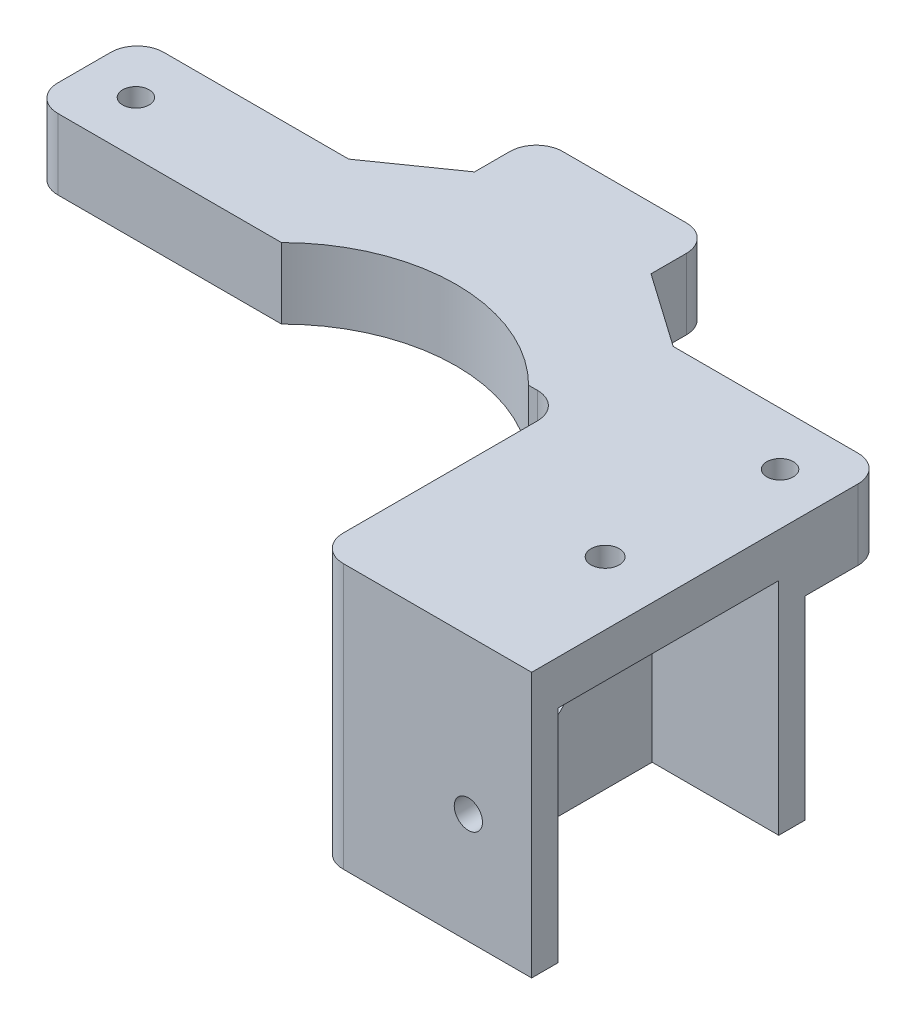
SolidWorks part; units mm, degrees
ref_plane "Front Plane" through (0, 0, 0) normal (0, 0, 1) x (1, 0, 0)
ref_plane "Top Plane" through (0, 0, 0) normal (0, 1, 0) x (1, 0, 0)
ref_plane "Right Plane" through (0, 0, 0) normal (1, 0, 0) x (0, 0, -1)
sketch "Sketch1" plane through (0, 0, 0) normal (0, 1, 0) x (1, 0, 0)
  point P0 (19.9354, 20.5827)
  line B0 (39.209, 44.4444) -> (22.0404, 42.2474)
  line B1 (45.8541, 73.4809) -> (45.8541, 51.994)
  line B2 (42.0529, 77.2821) -> (-35.0361, 77.2821)
  line B3 (-38.8372, 73.4809) -> (-38.8372, 51.994)
  line B4 (-32.1921, 44.4444) -> (-15.0236, 42.2474)
  arc B5 (19.8482, 42.7521) -> (-12.8313, 42.7521) centre (3.5084, 38.4289) ccw
  circle B6 centre (-16.4916, 46.356) radius 2.5
  circle B7 centre (-32.9916, 71.4109) radius 2.5
  circle B8 centre (40.0084, 71.4109) radius 2.5
  circle B9 centre (23.5084, 46.356) radius 2.5
  arc B10 (39.209, 44.4444) -> (45.8541, 51.994) centre (38.2429, 51.994) ccw
  arc B11 (-35.0361, 77.2821) -> (-38.8372, 73.4809) centre (-35.0361, 73.4809) ccw
  arc B12 (-38.8372, 51.994) -> (-32.1921, 44.4444) centre (-31.2261, 51.994) ccw
sketch_block_instance "ps3_eye_screws-1"
sketch_block "ps3_eye_screws"
sketch "Sketch2" plane through (0, 0, 0) normal (0, 1, 0) x (1, 0, 0)
  line L0 (3.5084, 38.4024) -> (3.5084, 55.3309) construction
  line L4 (-38.8372, 64.4109) -> (-14.8764, 64.4109)
  line L5 (-32.9916, 71.4109) -> (40.0084, 71.4109) construction
  line L6 (-32.9916, 71.4109) -> (-32.9916, 58.4109) construction
  line L7 (-32.9916, 58.4109) -> (40.0084, 58.4109) construction
  line L8 (40.0084, 71.4109) -> (40.0084, 58.4109) construction
  line L9 (-38.8372, 73.4809) -> (-38.8372, 51.994) construction
  line L10 (-14.8764, 64.4109) -> (-6.4916, 70.2821)
  line L11 (-6.4916, 70.2821) -> (-6.4916, 77.2821)
  line L12 (42.0529, 77.2821) -> (-35.0361, 77.2821) construction
  line L13 (-6.4916, 77.2821) -> (13.5084, 77.2821)
  line L14 (13.5084, 77.2821) -> (13.5084, 70.2821)
  line L15 (13.5084, 70.2821) -> (21.8933, 64.4109)
  line L16 (21.8933, 64.4109) -> (45.8541, 64.4109)
  line L17 (45.8541, 73.4809) -> (45.8541, 51.994) construction
  line L18 (45.8541, 64.4109) -> (45.8541, 52.4109)
  line L19 (45.8541, 52.4109) -> (17.5084, 52.4109)
  line L20 (-10.4916, 52.4109) -> (-38.8372, 52.4109)
  line L21 (-38.8372, 52.4109) -> (-38.8372, 64.4109)
  line L22 (3.5084, 55.3309) -> (3.5084, 77.2821) construction
  line L23 (-6.4916, 70.2821) -> (13.5084, 70.2821) construction
  line L24 (-32.9916, 58.4109) -> (-38.8372, 58.4109) construction
  line L25 (40.0084, 58.4109) -> (45.8541, 58.4109) construction
  circle A2 centre (-32.9916, 58.4109) radius 1.5
  circle A3 centre (40.0084, 58.4109) radius 1.5
  arc A4 (19.8482, 42.7521) -> (-12.8313, 42.7521) centre (3.5084, 38.4289) ccw construction
  arc A5 (-10.4916, 52.4109) -> (17.5084, 52.4109) centre (3.5084, 38.4024) cw
  point P27 (8.08, 39.4837)
  point P33 (3.5084, 42.9446)
  point P34 (3.5084, 38.4024)
  dimension "D1" = 3
  dimension "D7" = 28
  dimension "D8" = 19.805
  dimension "D2" = 13
  dimension "D3" = 145
  dimension "D4" = 145
  dimension "D5" = 20
  dimension "D6" = 12
  dimension "D9" = 7
extrude "Boss-Extrude1" add sketch "Sketch2" along normal blind 8
ref_plane "Plane1" through (0, 8, 0) normal (0, -1, 0) x (-1, 0, 0)
sketch "Sketch11" plane through (0, 8, 0) normal (0, -1, 0) x (-1, 0, 0)
  line L1 (14.4916, 55.4109) -> (38.8372, 55.4109)
  line L2 (14.4916, 55.4109) -> (14.4916, 24.4109)
  line L3 (14.4916, 24.4109) -> (38.8372, 24.4109)
  line L4 (38.8372, 55.4109) -> (38.8372, 24.4109)
  line L5 (38.8372, 73.4809) -> (38.8372, 51.994) construction
  circle A0 centre (32.9916, 58.4109) radius 1.5 construction
  point P6 (38.8372, 52.4109)
  point P8 (0, 0)
  point P9 (38.8372, 52.4109)
  point P10 (38.8372, 55.4109)
  dimension "D2" = 3
  dimension "D1" = 5
  dimension "D3" = 31
extrude "Boss-Extrude4" add sketch "Sketch11" along normal blind 30
sketch "Sketch12" plane through (-38.8372, 0, 0) normal (-1, 0, 0) x (0, 0, 1)
  line L0 (-24.4109, -22) -> (-55.4109, -22) construction
  line L1 (-52.4109, -22) -> (-27.4109, -22)
  line L2 (-52.4109, -22) -> (-52.4109, 3)
  line L3 (-52.4109, 3) -> (-27.4109, 3)
  line L4 (-27.4109, -22) -> (-27.4109, 3)
  line L5 (-55.4109, -22) -> (-55.4109, 0) construction
  dimension "D1" = 25
  dimension "D2" = 25
  dimension "D3" = 3
extrude "Cut-Extrude7" cut sketch "Sketch12" against normal offset from surface (14.3456 mm away) 10 up to face at (-14.4916, -4.6667, -44.0776)
sketch "Sketch13" plane through (-14.4916, 0, 0) normal (1, 0, 0) x (0, 0, -1)
  line L0 (52.4109, -22) -> (27.4109, 3) construction
  circle A0 centre (39.9109, -9.5) radius 3.1
  dimension "D1" = 6.2
extrude "Cut-Extrude8" cut sketch "Sketch13" against normal up to next
sketch "Sketch14" plane through (-14.4916, 0, 0) normal (1, 0, 0) x (0, 0, -1)
  circle A0 centre (39.9109, -9.5) radius 5
  dimension "D1" = 10
extrude "Cut-Extrude9" cut sketch "Sketch14" against normal blind 5.5
sketch "Sketch15" plane through (0, 0, -24.4109) normal (0, 0, 1) x (1, 0, 0)
  line L0 (-31.6644, -22) -> (-31.6644, 3) construction
  line L1 (-24.4916, 3) -> (-38.8372, 3) construction
  line L2 (-14.4916, -22) -> (-38.8372, -22) construction
  circle A0 centre (-31.6644, -9.5) radius 1.6
  point P6 (-31.6644, 3)
  point P9 (-34.4877, -22)
  dimension "D1" = 3.2
extrude "Cut-Extrude10" cut sketch "Sketch15" against normal blind 5.5
sketch "Sketch16" plane through (0, 8, 0) normal (0, 1, 0) x (1, 0, 0)
  line L0 (-31.6644, 52.4109) -> (-31.6644, 27.4109) construction
  line L1 (-24.4916, 52.4109) -> (-38.8372, 52.4109) construction
  line L2 (-24.4916, 27.4109) -> (-38.8372, 27.4109) construction
  circle A0 centre (-31.6644, 39.9109) radius 1.6
  dimension "D1" = 3.2
extrude "Cut-Extrude11" cut sketch "Sketch16" against normal up to next contours A0
sketch "Sketch17" plane through (0, 0, 0) normal (0, -1, 0) x (1, 0, 0)
  line L0 (-38.8372, -55.4109) -> (-14.4916, -55.4109) construction
  line L1 (-31.2595, -61.4109) -> (-29.5275, -58.4109)
  line L2 (-29.5275, -58.4109) -> (-31.2595, -55.4109)
  line L3 (-31.2595, -55.4109) -> (-34.7236, -55.4109)
  line L4 (-34.7236, -55.4109) -> (-36.4557, -58.4109)
  line L5 (-36.4557, -58.4109) -> (-34.7236, -61.4109)
  line L6 (-34.7236, -61.4109) -> (-31.2595, -61.4109)
  line L8 (38.2764, -61.4109) -> (41.7405, -61.4109)
  line L9 (41.7405, -61.4109) -> (43.4725, -58.4109)
  line L10 (43.4725, -58.4109) -> (41.7405, -55.4109)
  line L11 (41.7405, -55.4109) -> (38.2764, -55.4109)
  line L12 (38.2764, -55.4109) -> (36.5443, -58.4109)
  line L13 (36.5443, -58.4109) -> (38.2764, -61.4109)
  circle A0 centre (-32.9916, -58.4109) radius 3 construction
  circle A1 centre (40.0084, -58.4109) radius 3 construction
extrude "Cut-Extrude12" cut sketch "Sketch17" against normal blind 2.6
fillet "Fillet2" radius 3 7 edges at (-14.4916, 4, -52.4109) (-14.4916, -7, -24.4109) (45.8541, 4, -52.4109) (45.8541, 4, -64.4109) (13.5084, 4, -77.2821) (-6.4916, 4, -77.2821) (-38.8372, 4, -64.4109)
mirror "Mirror2" about plane through (45.8541, 8, -64.4109) normal (-1, 0, 0) of bodies 116
delete or keep bodies "Body-Delete/Keep 1" type keep bodies bodies 118
